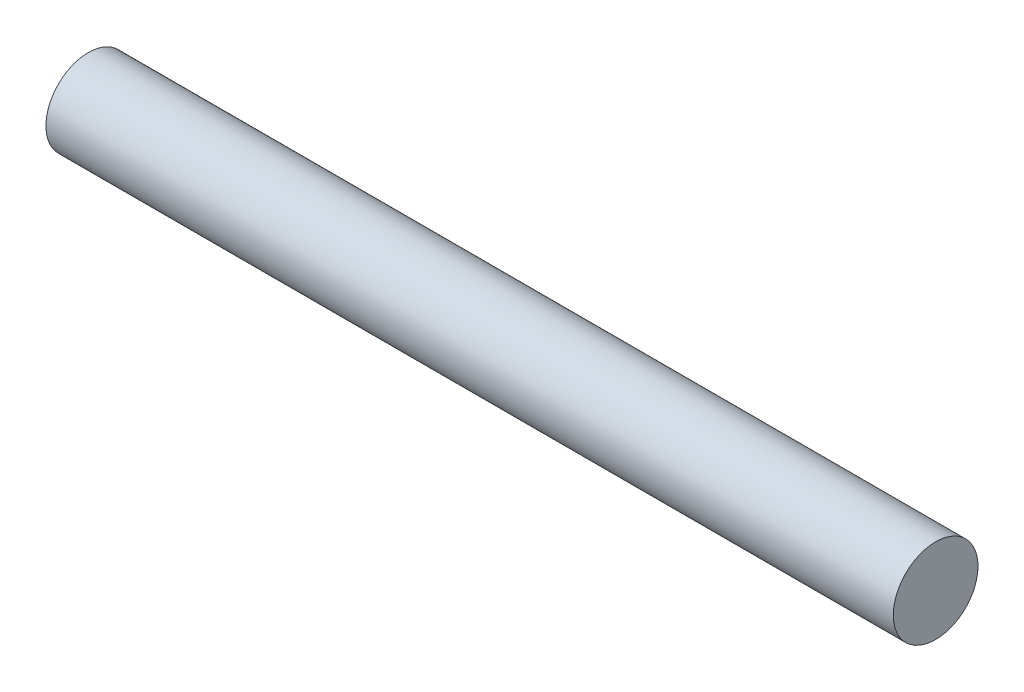
SolidWorks part; units mm, degrees
ref_plane "Front Plane" through (0, 0, 0) normal (0, 0, 1) x (1, 0, 0)
ref_plane "Top Plane" through (0, 0, 0) normal (0, 1, 0) x (1, 0, 0)
ref_plane "Right Plane" through (0, 0, 0) normal (1, 0, 0) x (0, 0, -1)
sketch "Sketch1" plane through (0, 0, 0) normal (1, 0, 0) x (0, 0, -1)
  circle A0 centre (0, 0) radius 3.175
  dimension "D1" = 6.35
extrude "main" add sketch "Sketch1" along normal mid plane 63.5
